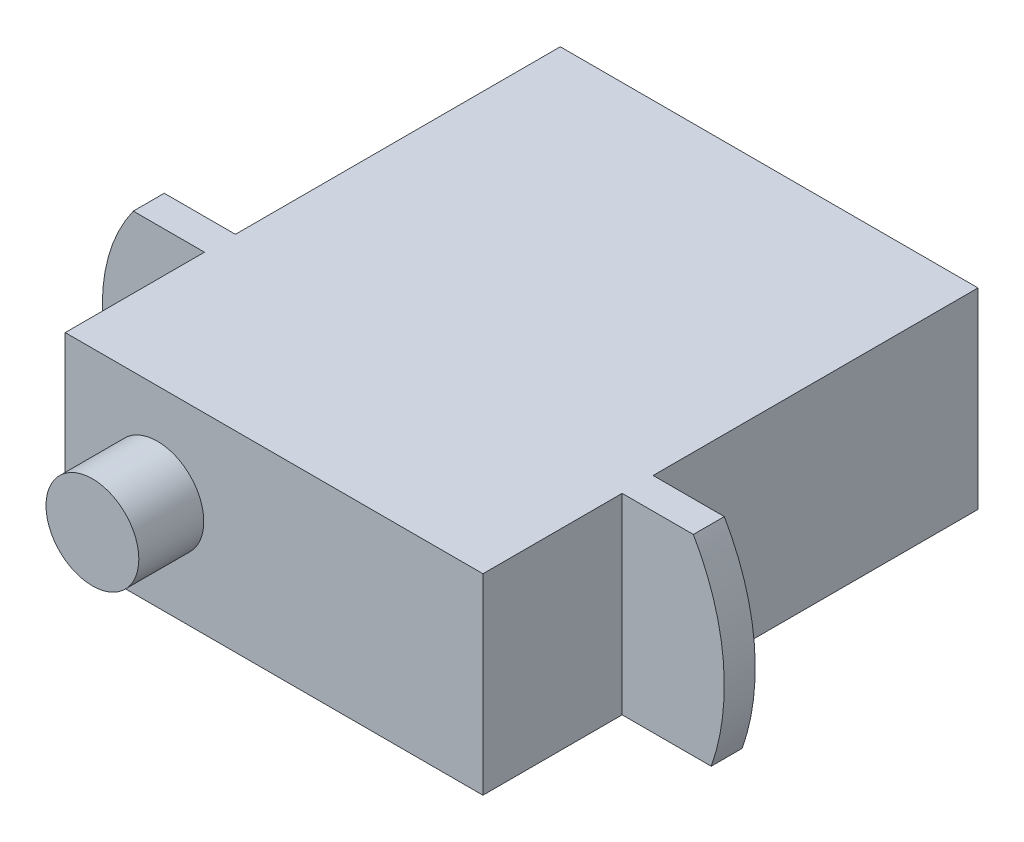
SolidWorks part; units mm, degrees
ref_plane "Front" through (0, 0, 0) normal (0, 0, 1) x (1, 0, 0)
ref_plane "Top" through (0, 0, 0) normal (0, 1, 0) x (1, 0, 0)
ref_plane "Right" through (0, 0, 0) normal (1, 0, 0) x (0, 0, -1)
sketch "草图1" plane through (0, 0, 0) normal (0, 1, 0) x (1, 0, 0)
  line L0 (-16.3779, 7.1628) -> (-2.8779, 7.1628)
  line L1 (-2.8779, 7.1628) -> (-2.8779, -8.8372)
  line L2 (-16.3779, 7.1628) -> (-16.3779, -8.8372)
  line L3 (-16.3779, -8.8372) -> (-2.8779, -8.8372)
  dimension "D1" = 13.5
  dimension "D2" = 16
extrude "凸台-拉伸1" add sketch "草图1" along normal blind 6.2
sketch "草图2" plane through (0, 0, 8.8372) normal (0, 0, 1) x (1, 0, 0)
  circle A0 centre (-13.3994, 3.1484) radius 1.5
  dimension "D1" = 3
extrude "凸台-拉伸2" add sketch "草图2" along normal blind 2.1
sketch "草图3" plane through (-16.3779, 0, 0) normal (-1, 0, 0) x (0, 0, 1)
  line L0 (8.8372, 1.6484) -> (8.8372, 4.6484) construction
  line L1 (3.3372, 6.2) -> (4.3372, 6.2)
  line L2 (3.3372, 6.2) -> (3.3372, 0)
  line L3 (3.3372, 0) -> (4.3372, 0)
  line L4 (4.3372, 6.2) -> (4.3372, 0)
  line L5 (3.3372, 6.2) -> (4.3372, 0) construction
  line L6 (3.3372, 0) -> (4.3372, 6.2) construction
  line L7 (-7.1628, 6.2) -> (8.8372, 6.2) construction
  point P0 (3.8372, 3.1)
  dimension "D1" = 4.5
  dimension "D2" = 1
  dimension "D3" = 6.2
extrude "凸台-拉伸3" add sketch "草图3" along normal blind 3.3
sketch "草图5" plane through (0, 0, 4.3372) normal (0, 0, 1) x (1, 0, 0)
  line L0 (-19.6779, 6.2) -> (-16.3779, 6.2) construction
  line L1 (-19.6779, 0) -> (-16.3779, 0) construction
  line L2 (-18.6779, 6.2) -> (-19.6779, 6.2)
  line L3 (-19.6779, 6.2) -> (-19.6779, 3.1)
  line L4 (-19.6779, 3.1) -> (-19.6779, 0)
  line L5 (-19.6779, 0) -> (-18.6779, 0)
  arc A0 (-18.6779, 6.2) -> (-18.6779, 0) centre (-14.3729, 3.1) ccw
  line M2 (-16.3779, 6.2) -> (-19.6779, 6.2)
  line M3 (-19.6779, 6.2) -> (-19.6779, 0)
  line M4 (-19.6779, 0) -> (-16.3779, 0)
  dimension "D1" = 1
extrude "切除-拉伸1" cut sketch "草图5" against normal blind 4 contours A0 M2 M3 | A0 M3 M4
sketch "草图6" plane through (-2.8779, 0, 0) normal (1, 0, 0) x (0, 0, -1)
  line L0 (-8.8372, 0) -> (7.1628, 0) construction
  line L1 (7.1628, 0) -> (7.1628, 6.2) construction
  line L2 (7.1628, 6.2) -> (-8.8372, 6.2) construction
  line L3 (-8.8372, 6.2) -> (-8.8372, 0) construction
  line L4 (-3.3372, 0) -> (-3.3372, 6.2) construction
  line L5 (-3.3372, 0) -> (-4.3372, 0) construction
  line L6 (-4.3372, 6.2) -> (-4.3372, 0) construction
  line L7 (-4.3372, 6.2) -> (-3.3372, 6.2) construction
  line L8 (-8.8372, 0) -> (7.1628, 0)
  line L9 (7.1628, 0) -> (7.1628, 6.2)
  line L10 (7.1628, 6.2) -> (-8.8372, 6.2)
  line L11 (-8.8372, 6.2) -> (-8.8372, 0)
  line L12 (-3.3372, 0) -> (-3.3372, 6.2)
  line L13 (-3.3372, 0) -> (-4.3372, 0)
  line L14 (-4.3372, 6.2) -> (-4.3372, 0)
  line L15 (-4.3372, 6.2) -> (-3.3372, 6.2)
extrude "凸台-拉伸4" add sketch "草图6" along normal blind 3.3 contours L10 L14 L8 L12
sketch "草图10" plane through (0, 0, 4.3372) normal (0, 0, 1) x (1, 0, 0)
  line L0 (0.4221, 6.2) -> (-2.8779, 6.2) construction
  line L1 (-0.5779, 6.2) -> (0.4221, 6.2)
  line L2 (0.4221, 6.2) -> (0.4221, 0)
  line L3 (0.4221, 0) -> (0, 0)
  arc A0 (-0.5779, 6.2) -> (0, 0) centre (-7.0272, 2.4719) cw
  dimension "D1" = 1
extrude "切除-拉伸2" cut sketch "草图10" against normal blind 4
